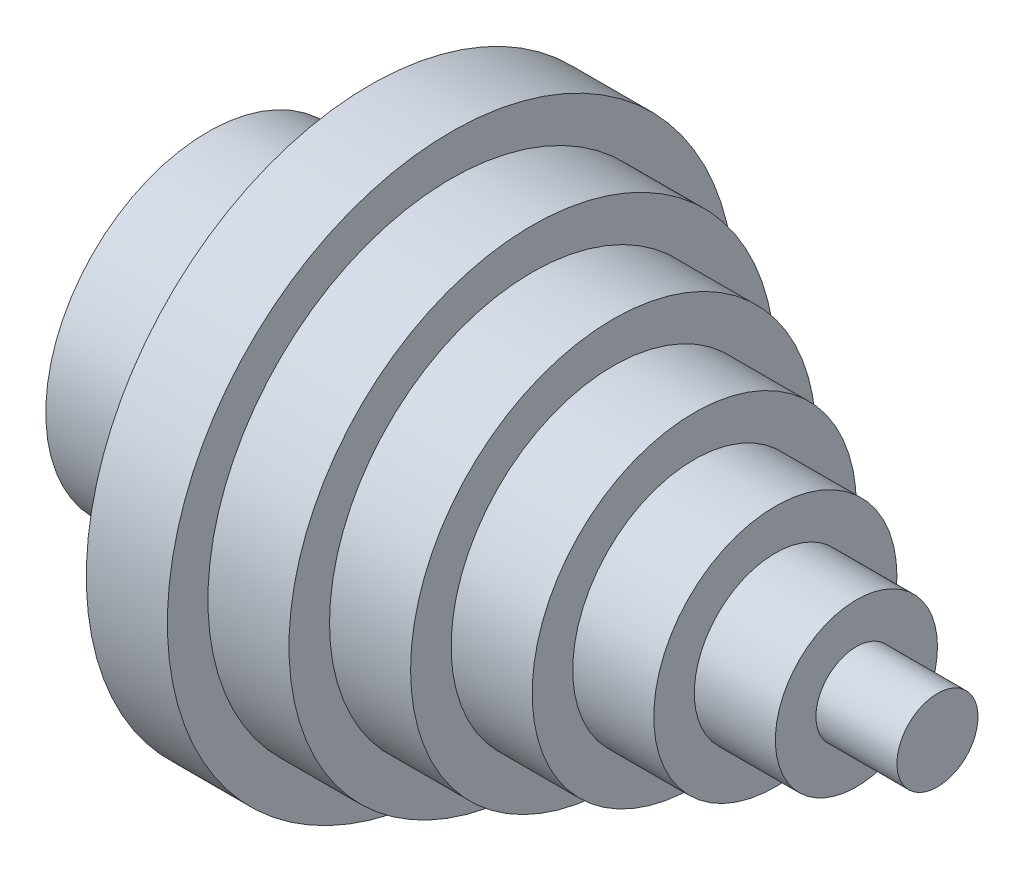
SolidWorks part; units mm, degrees
ref_plane "Front Plane" through (0, 0, 0) normal (0, 0, 1) x (1, 0, 0)
ref_plane "Top Plane" through (0, 0, 0) normal (0, 1, 0) x (1, 0, 0)
ref_plane "Right Plane" through (0, 0, 0) normal (1, 0, 0) x (0, 0, -1)
sketch "Sketch1" plane through (0, 0, 0) normal (0, 0, 1) x (1, 0, 0)
  line L0 (0, 0) -> (-218.6884, 0) construction
  line L1 (0, 0) -> (0, 10)
  line L2 (0, 10) -> (-20, 10)
  line L3 (-20, 10) -> (-20, 20)
  line L4 (-20, 20) -> (-40, 20)
  line L5 (-40, 20) -> (-40, 30)
  line L6 (-40, 30) -> (-60, 30)
  line L7 (-60, 30) -> (-60, 40)
  line L8 (-60, 40) -> (-80, 40)
  line L9 (-80, 40) -> (-80, 50)
  line L10 (-80, 50) -> (-100, 50)
  line L11 (-100, 50) -> (-100, 60)
  line L12 (-100, 60) -> (-120, 60)
  line L13 (-120, 60) -> (-120, 70)
  line L14 (-120, 70) -> (-140, 70)
  line L15 (-140, 70) -> (-140, 40)
  line L16 (-140, 40) -> (-180, 40)
  line L17 (-180, 40) -> (-180, 0)
  line L18 (0, 0) -> (-180, 0)
  dimension "D2" = 20
  dimension "D3" = 80
  dimension "D4" = 140
  dimension "D5" = 120
  dimension "D6" = 100
  dimension "D7" = 80
  dimension "D8" = 60
  dimension "D9" = 40
  dimension "D10" = 20
  dimension "D11" = 180
  dimension "D16" = 40
revolve "Revolve1" add sketch "Sketch1" angle 360 about L0
sketch "Sketch2" plane through (-180, 0, 0) normal (-1, 0, 0) x (0, 0, 1)
  circle A0 centre (0, 0) radius 30
extrude "Cut-Extrude1" cut sketch "Sketch2" against normal up to surface (40 mm away) up to face at (-140, 0, -40)
